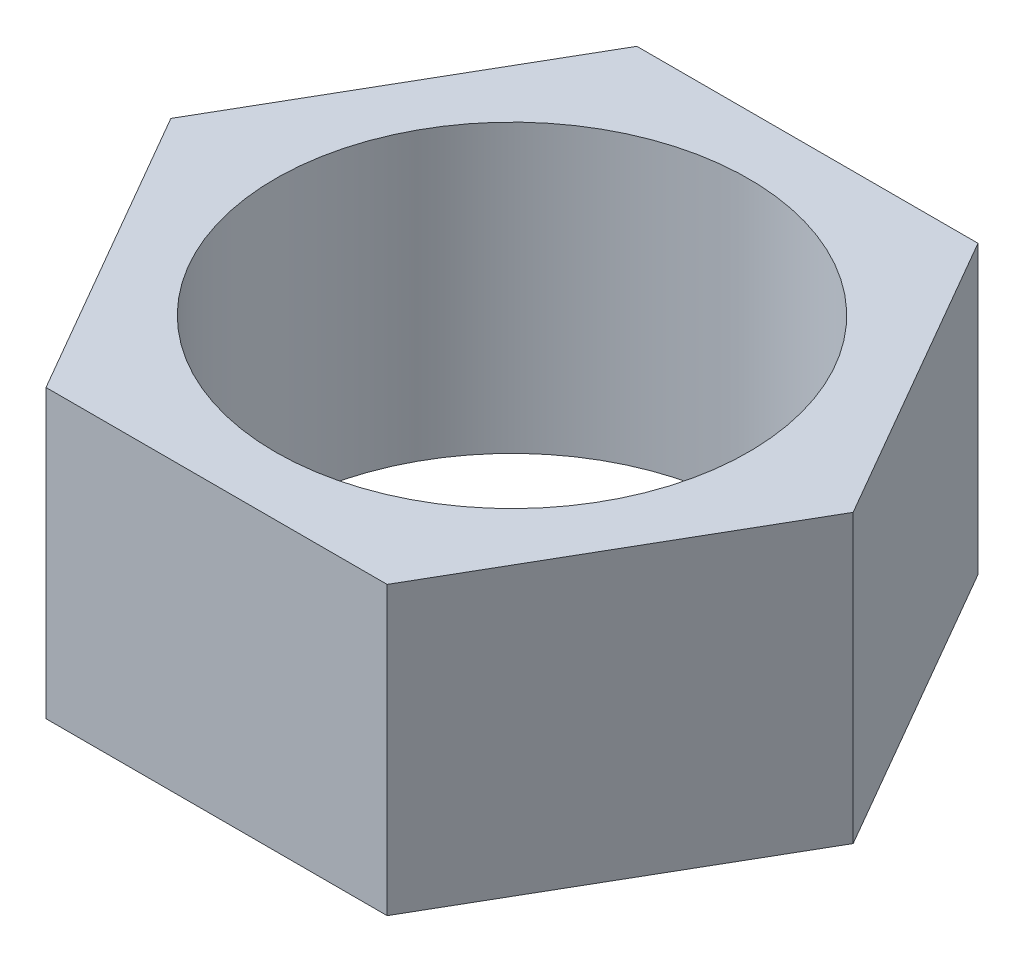
SolidWorks part; units mm, degrees
ref_plane "Alzado" through (0, 0, 0) normal (0, 0, 1) x (1, 0, 0)
ref_plane "Planta" through (0, 0, 0) normal (0, 1, 0) x (1, 0, 0)
ref_plane "Vista lateral" through (0, 0, 0) normal (1, 0, 0) x (0, 0, -1)
sketch "Croquis1" plane through (0, 0, 0) normal (0, 1, 0) x (1, 0, 0)
  line L1 (2.3782, 0) -> (1.1891, 2.0596)
  line L2 (1.1891, 2.0596) -> (-1.1891, 2.0596)
  line L3 (-1.1891, 2.0596) -> (-2.3782, 0)
  line L4 (-2.3782, 0) -> (-1.1891, -2.0596)
  line L5 (-1.1891, -2.0596) -> (1.1891, -2.0596)
  line L6 (1.1891, -2.0596) -> (2.3782, 0)
  circle A0 centre (0, 0) radius 1.65
  circle A1 centre (0, 0) radius 2.0596 construction
  dimension "D1" = 3.3
extrude "Saliente-Extruir1" add sketch "Croquis1" along normal blind 2
